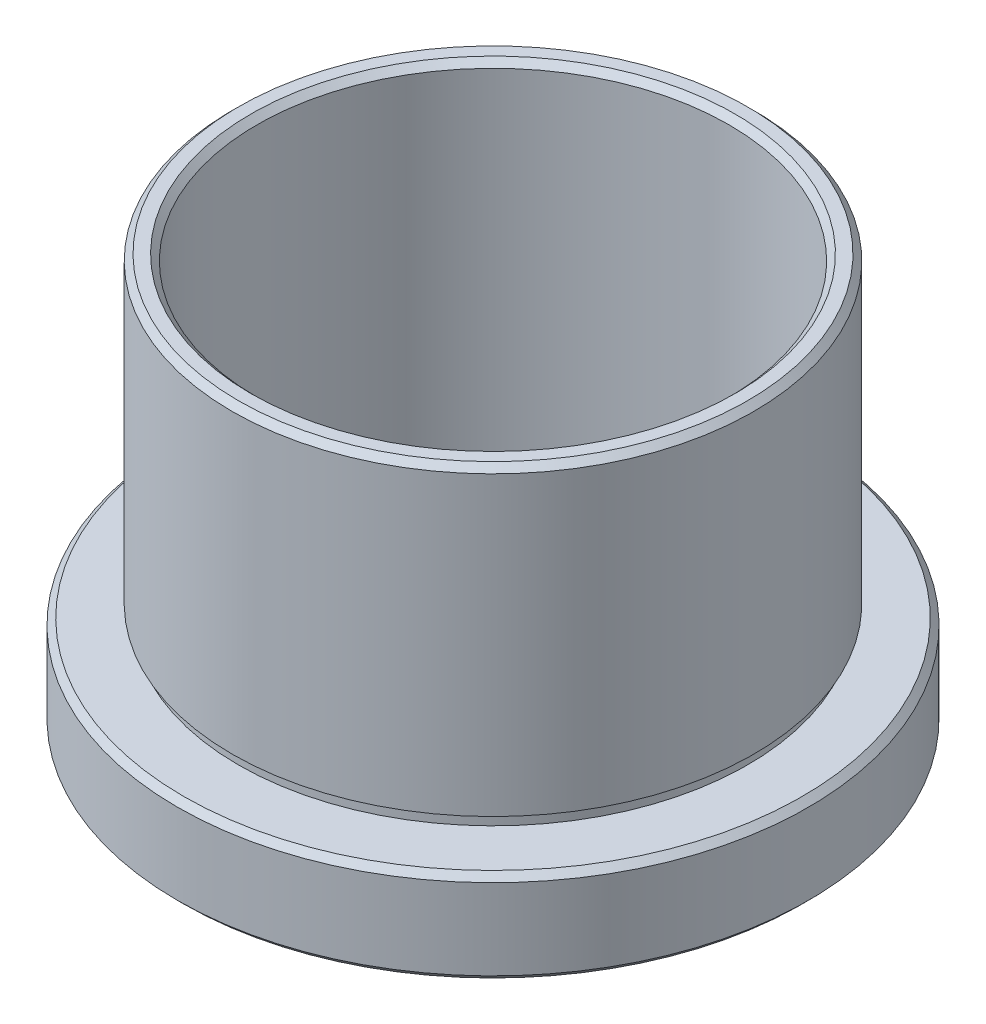
SolidWorks part; units mm, degrees
ref_plane "前视基准面" through (0, 0, 0) normal (0, 0, 1) x (1, 0, 0)
ref_plane "上视基准面" through (0, 0, 0) normal (0, 1, 0) x (1, 0, 0)
ref_plane "右视基准面" through (0, 0, 0) normal (1, 0, 0) x (0, 0, -1)
sketch "草图1" plane through (0, 0, 0) normal (0, 0, 1) x (1, 0, 0)
  line L0 (0, 44.5986) -> (0, -38.4055) construction
  line L1 (19.5, 27.0429) -> (20.5, 27.0429)
  line L2 (21, 26.5429) -> (21, 2.6429)
  line L3 (21, 2.6429) -> (20.5, 2.6429)
  line L4 (20.5, 2.6429) -> (20.5, 1.6429)
  line L5 (20.5, 1.6429) -> (24.9, 1.6429)
  line L6 (25.4, 1.1429) -> (25.4, -5.3571)
  line L7 (24.9, -5.8571) -> (21.5, -5.8571)
  line L8 (21, -5.3571) -> (21, -1.3571)
  line L9 (21, -1.3571) -> (21.1, -1.3571)
  line L10 (21.1, -1.3571) -> (21.1, -0.3571)
  line L11 (25.4, -5.3571) -> (24.9, -5.8571)
  line L12 (19, -0.3571) -> (19, 26.5429)
  line L13 (21.1, -0.3571) -> (19, -0.3571)
  line L14 (21.5, -5.8571) -> (21, -5.3571)
  line L15 (20.5, 27.0429) -> (21, 26.5429)
  line L16 (19, 26.5429) -> (19.5, 27.0429)
  line L17 (24.9, 1.6429) -> (25.4, 1.1429)
  point P3 (19, 27.0429)
  point P4 (21, 27.0429)
  point P9 (25.4, -5.8571)
  point P10 (25.4, 1.6429)
  point P11 (21, -5.8571)
  point P13 (20.5, 2.1429)
  point P14 (21.1, -0.8571)
  dimension "D2" = 25.4
  dimension "D3" = 21
  dimension "D4" = 21
  dimension "D5" = 19
  dimension "D6" = 7.5
  dimension "D7" = 5.5
  dimension "D8" = 1
  dimension "D9" = 1
  dimension "D10" = 20.5
  dimension "D11" = 21.1
revolve "旋转2" add sketch "草图1" angle 360 about L0
